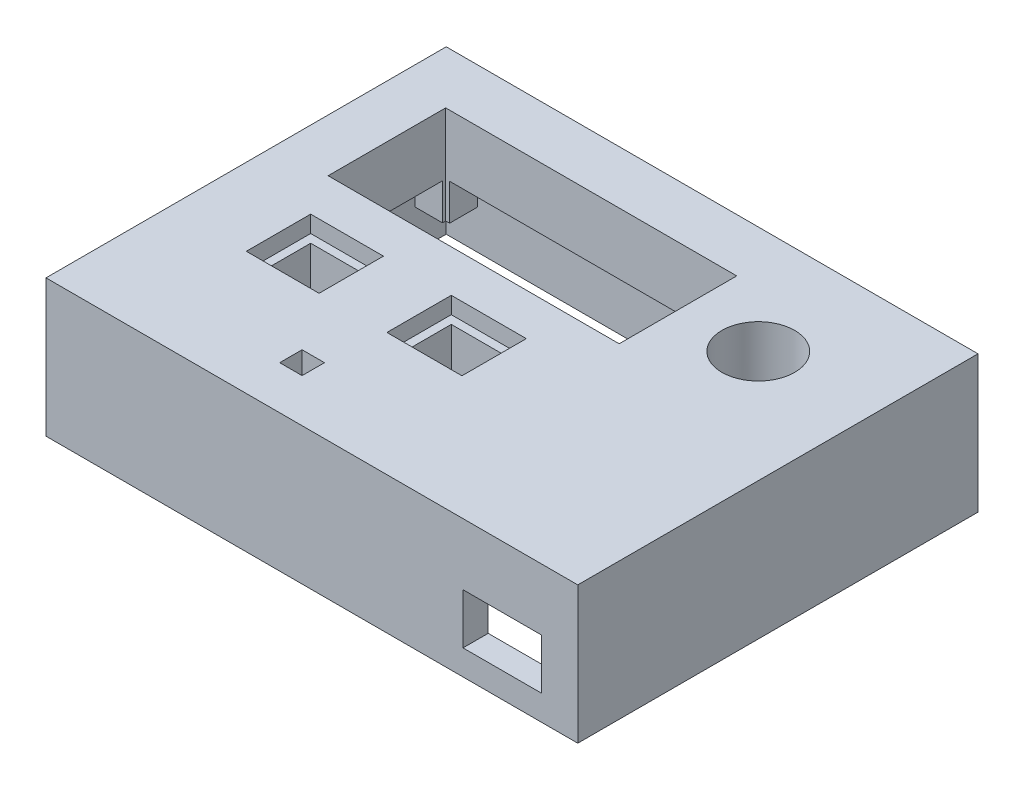
SolidWorks part; units mm, degrees
ref_plane "Front Plane" through (0, 0, 0) normal (0, 0, 1) x (1, 0, 0)
ref_plane "Top Plane" through (0, 0, 0) normal (0, 1, 0) x (1, 0, 0)
ref_plane "Right Plane" through (0, 0, 0) normal (1, 0, 0) x (0, 0, -1)
sketch "Sketch1" plane through (0, 0, 0) normal (0, 1, 0) x (1, 0, 0)
  line L6 (46, 35.75) -> (48, 35.75)
  line L7 (-8.1, -13.75) -> (-8.1, -2.25)
  line L8 (-8.1, -2.25) -> (5.3066, -2.25)
  line L9 (-37.6, 26.25) -> (14.4, 26.25)
  line L10 (-37.6, 26.25) -> (-37.6, 5.25)
  line L11 (-37.6, 5.25) -> (14.4, 5.25)
  line L12 (14.4, 26.25) -> (14.4, 5.25)
  line L14 (-33.217, -13.75) -> (-33.217, -2.25)
  line L15 (-33.217, -2.25) -> (-20.217, -2.25)
  line L16 (-20.217, -13.75) -> (-20.217, -2.25)
  line L22 (5.3066, -13.75) -> (5.3066, -2.25)
  line L24 (-11, -29) -> (-14, -29)
  line L25 (-14, -29) -> (-14, -23)
  line L26 (-14, -23) -> (-8, -23)
  line L27 (-8, -23) -> (-8, -29)
  line L28 (-8, -29) -> (-11, -29)
  line L29 (-47, -35.75) -> (45, -35.75)
  line L30 (-47, 33.75) -> (-47, -33.75)
  line L31 (45, 35.75) -> (46, 35.75)
  line L32 (-47, 33.75) -> (-47, 35.75)
  line L33 (-47, 35.75) -> (45, 35.75)
  line L38 (-47, -33.75) -> (-47, -35.75)
  line L40 (46, -35.75) -> (45, -35.75)
  line L41 (48, 35.75) -> (48, -35.75)
  line L42 (48, -35.75) -> (46, -35.75)
  line L43 (-33.217, -13.75) -> (-20.217, -13.75)
  line L44 (-8.1, -13.75) -> (5.3066, -13.75)
  circle A0 centre (28, 16.5) radius 6.5
  point P0 (0, 0)
  dimension "D7" = 13
  dimension "D2" = 2
  dimension "D3" = 7.5
  dimension "D5" = 52
  dimension "D6" = 21
  dimension "D9" = 1
  dimension "D11" = 29.5
  dimension "D13" = 7.5
  dimension "D14" = 3
  dimension "D15" = 3
  dimension "D16" = 6
  dimension "D19" = 2
extrude "Boss-Extrude1" add sketch "Sketch1" along normal blind 3
sketch "Sketch2" plane through (0, 0, 0) normal (0, -1, 0) x (1, 0, 0)
  line L0 (41.5, -31.25) -> (40.5, -31.25)
  line L1 (40.5, -31.25) -> (-42.5, -31.25)
  line L3 (40.5, 31.25) -> (-42.5, 31.25)
  line L4 (-42.5, -31.25) -> (-42.5, 31.25)
  line L8 (48, 35.75) -> (48, -35.75)
  line L13 (-47, 35.75) -> (-47, -35.75)
  line L23 (40.5, 31.25) -> (41.5, 31.25)
  line L28 (-47, 35.75) -> (48, 35.75)
  line L30 (41.5, 31.25) -> (43.5, 31.25)
  line L31 (43.5, 31.25) -> (43.5, -31.25)
  line L32 (43.5, -31.25) -> (41.5, -31.25)
  line L33 (-47, -35.75) -> (48, -35.75)
  dimension "D1" = 1
  dimension "D2" = 2
extrude "Boss-Extrude2" add sketch "Sketch2" along normal blind 21.5
sketch "Sketch3" plane through (0, 0, 0) normal (0, -1, 0) x (1, 0, 0)
  line L0 (-37.6, -26.25) -> (-37.6, -5.25) construction
  line L1 (-37.6, -26.25) -> (14.4, -26.25) construction
  line L2 (-38.8, -25.6758) -> (-42.5, -25.6758)
  line L3 (-42.5, 31.25) -> (-42.5, -31.25) construction
  line L4 (-38.8, -25.6758) -> (-37.6, -25.6758)
  line L5 (-37.6, -26.25) -> (-37.6, -5.25) construction
  line L6 (-37.6, -25.6758) -> (-37.6, -26.25)
  line L7 (-36.9029, -27.93) -> (-36.9029, -26.25)
  line L8 (-37.6, -26.25) -> (14.4, -26.25) construction
  line L9 (-36.9029, -26.25) -> (-37.6, -26.25)
  line L10 (-36.9029, -27.93) -> (-36.9029, -31.25)
  line L11 (-42.5, -31.25) -> (43.5, -31.25) construction
  line L12 (-36.9029, -31.25) -> (-42.5, -31.25)
  line L13 (-42.5, -31.25) -> (-42.5, -25.6758)
  line L14 (43.5, -25.2705) -> (36.0216, -25.2705)
  line L15 (43.5, -31.25) -> (43.5, 31.25) construction
  line L16 (36.0216, -25.2705) -> (36.0216, -31.25)
  line L17 (-42.5, -31.25) -> (43.5, -31.25) construction
  line L18 (36.0216, -31.25) -> (43.5, -31.25)
  line L19 (43.5, -31.25) -> (43.5, -25.2705)
  line L20 (15.5674, 31.25) -> (15.5674, 24.7212)
  line L21 (43.5, 31.25) -> (-42.5, 31.25) construction
  line L22 (15.5674, 24.7212) -> (21.541, 24.7212)
  line L23 (21.541, 24.7212) -> (21.541, 31.25)
  line L24 (21.541, 31.25) -> (15.5674, 31.25)
  circle A1 centre (-38.8, -27.93) radius 1.25
  circle A2 centre (39.43, -27.68) radius 1.25
  circle A3 centre (18.47, 27.69) radius 1.25
  dimension "D1" = 2.5
  dimension "D4" = 2.5
  dimension "D6" = 2.5
  dimension "D2" = 1.2
  dimension "D3" = 1.68
  dimension "D5" = 55.37
  dimension "D7" = 20.96
  dimension "D8" = 78.23
extrude "Boss-Extrude3" add sketch "Sketch3" along normal blind 14.5
sketch "Sketch4" plane through (0, 0, 35.75) normal (0, 0, 1) x (1, 0, 0)
  line L0 (48, 3) -> (48, -21.5) construction
  line L2 (27.5, -8) -> (41.5, -8)
  line L4 (27.5, -8) -> (27.5, -17)
  line L5 (27.5, -17) -> (41.5, -17)
  line L6 (41.5, -8) -> (41.5, -17)
  line L7 (48, -21.5) -> (-47, -21.5) construction
  dimension "D1" = 14
  dimension "D2" = 9
  dimension "D3" = 6.5
  dimension "D4" = 4.5
extrude "Cut-Extrude1" cut sketch "Sketch4" against normal up to next
sketch "Sketch5" plane through (0, 0, 0) normal (0, -1, 0) x (1, 0, 0)
  line L0 (-37.6, -5.25) -> (14.4, -5.25) construction
  line L1 (-39.6, -3.25) -> (16.4, -3.25)
  line L2 (-39.6, -3.25) -> (-39.6, -28.25)
  line L3 (-39.6, -28.25) -> (16.4, -28.25)
  line L4 (16.4, -3.25) -> (16.4, -28.25)
  line L5 (14.4, -26.25) -> (14.4, -5.25) construction
  line L6 (-36.9029, -26.25) -> (14.4, -26.25) construction
  line L7 (-37.6, -26.25) -> (-37.6, -5.25) construction
  line L9 (-37.6, -5.25) -> (14.4, -5.25)
  line L10 (-37.6, -5.25) -> (-37.6, -26.25)
  line L11 (-37.6, -26.25) -> (14.4, -26.25)
  line L12 (14.4, -5.25) -> (14.4, -26.25)
  circle A0 centre (28, -16.5) radius 6.5
  circle A1 centre (28, -16.5) radius 8.5
  dimension "D5" = 2
  dimension "D1" = 2
  dimension "D2" = 2
  dimension "D3" = 2
  dimension "D4" = 2
extrude "Boss-Extrude4" add sketch "Sketch5" along normal blind 8 contours L2 L1 L4 L3 | L10 L9 L12 L11 | A1 | A0
sketch "Sketch7" plane through (0, 3, 0) normal (0, 1, 0) x (1, 0, 0)
  line L0 (-14, -23) -> (-8, -23) construction
  line L1 (-13, -28) -> (-9, -28)
  line L2 (-13, -28) -> (-13, -24)
  line L3 (-13, -24) -> (-9, -24)
  line L4 (-9, -28) -> (-9, -24)
  line L5 (-11, -29) -> (-14, -29) construction
  line L6 (-8, -23) -> (-8, -29) construction
  line L7 (-14, -29) -> (-14, -23) construction
  line L9 (-14, -29) -> (-8, -29)
  line L10 (-14, -29) -> (-14, -23)
  line L11 (-14, -23) -> (-8, -23)
  line L12 (-8, -29) -> (-8, -23)
  dimension "D1" = 1
  dimension "D2" = 1
  dimension "D3" = 1
  dimension "D4" = 1
extrude "Boss-Extrude5" add sketch "Sketch7" against normal blind 13
sketch "Sketch8" plane through (0, 0, 0) normal (0, -1, 0) x (1, 0, 0)
  line L0 (-33.217, 2.25) -> (-20.217, 2.25) construction
  line L2 (-33.217, 12.25) -> (-33.217, 2.25)
  line L3 (-33.217, 2.25) -> (-20.217, 2.25)
  line L4 (-20.217, 12.25) -> (-20.217, 2.25)
  line L6 (-8.1, 13.75) -> (-8.1, 2.25)
  line L7 (-8.1, 2.25) -> (5.3066, 2.25)
  line L8 (5.3066, 13.75) -> (5.3066, 2.25)
  line L9 (-31.717, 12.25) -> (-21.717, 12.25)
  line L10 (-31.717, 12.25) -> (-31.717, 3.75)
  line L11 (-31.717, 3.75) -> (-21.717, 3.75)
  line L12 (-21.717, 12.25) -> (-21.717, 3.75)
  line L13 (-6.6, 12.25) -> (3.8066, 12.25)
  line L14 (-6.6, 12.25) -> (-6.6, 3.75)
  line L15 (-6.6, 3.75) -> (3.8066, 3.75)
  line L16 (3.8066, 12.25) -> (3.8066, 3.75)
  line L19 (-8.1, 13.75) -> (5.3066, 13.75)
  line L20 (-33.217, 12.25) -> (-33.217, 13.75)
  line L21 (-33.217, 13.75) -> (-33.217, 2.25) construction
  line L22 (-33.217, 13.75) -> (-20.217, 13.75)
  line L23 (-20.217, 13.75) -> (-20.217, 2.25) construction
  line L24 (-20.217, 13.75) -> (-20.217, 12.25)
  dimension "D1" = 1.5
  dimension "D2" = 1.5
  dimension "D3" = 1.5
  dimension "D4" = 1.5
  dimension "D6" = 1.5
  dimension "D7" = 1.5
  dimension "D8" = 1.5
extrude "Boss-Extrude6" add sketch "Sketch8" along normal blind 9 separate body
sketch "Sketch9" plane through (0, 0, 0) normal (0, -1, 0) x (1, 0, 0)
  line L0 (-33.217, 13.75) -> (-20.217, 13.75) construction
  line L5 (-10.1, 15.75) -> (7.3066, 15.75)
  line L6 (-10.1, 15.75) -> (-10.1, 0.25)
  line L7 (-10.1, 0.25) -> (7.3066, 0.25)
  line L8 (7.3066, 15.75) -> (7.3066, 0.25)
  line L9 (-33.217, 13.75) -> (-20.217, 13.75)
  line L10 (-33.217, 13.75) -> (-33.217, 2.25)
  line L11 (-33.217, 2.25) -> (-20.217, 2.25)
  line L12 (-8.1, 13.75) -> (-8.1, 2.25) construction
  line L14 (5.3066, 13.75) -> (5.3066, 2.25) construction
  line L15 (-8.1, 2.25) -> (5.3066, 2.25) construction
  line L23 (-8.1, 2.25) -> (5.3066, 2.25)
  line L25 (-20.217, 13.75) -> (-20.217, 2.25)
  line L26 (-35.217, 15.75) -> (-18.217, 15.75)
  line L27 (-35.217, 15.75) -> (-35.217, 0.25)
  line L28 (-35.217, 0.25) -> (-18.217, 0.25)
  line L29 (-18.217, 15.75) -> (-18.217, 0.25)
  line L30 (-33.217, 13.75) -> (-33.217, 2.25) construction
  line L32 (-8.1, 13.75) -> (5.3066, 13.75)
  line L33 (-8.1, 13.75) -> (-8.1, 2.25)
  line L34 (5.3066, 2.25) -> (5.3066, 13.75)
  dimension "D1" = 2
  dimension "D2" = 2
  dimension "D3" = 2
  dimension "D4" = 2
  dimension "D5" = 2
  dimension "D6" = 2
  dimension "D7" = 2
  dimension "D8" = 2
extrude "Boss-Extrude7" add sketch "Sketch9" along normal blind 3
sketch "Sketch10" plane through (0, -8, 0) normal (0, -1, 0) x (1, 0, 0)
  line L0 (-39.6, -28.25) -> (-39.6, -26.9695)
  line L1 (-39.6, -28.25) -> (-37.5917, -28.25)
  arc A0 (-39.6, -26.9695) -> (-37.5917, -28.25) centre (-38.8, -27.93) cw
extrude "Cut-Extrude2" cut sketch "Sketch10" against normal blind 5
